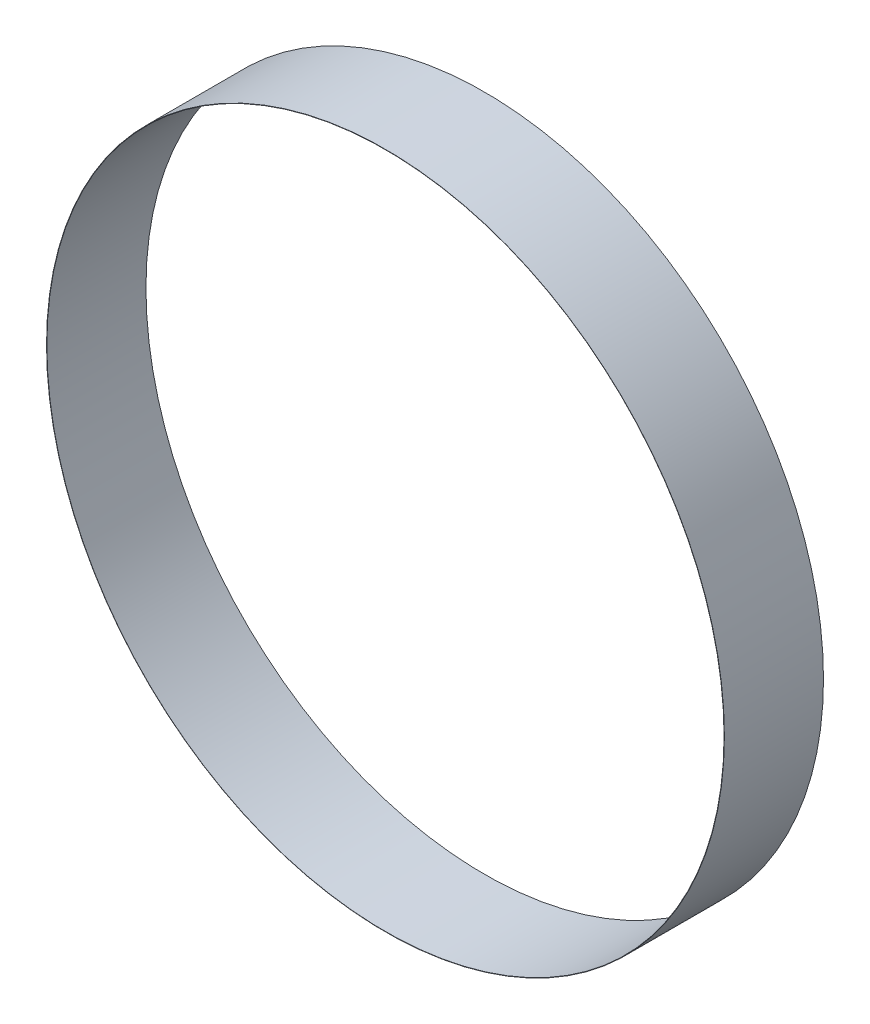
SolidWorks part; units mm, degrees
ref_plane "前视基准面" through (0, 0, 0) normal (0, 0, 1) x (1, 0, 0)
ref_plane "上视基准面" through (0, 0, 0) normal (0, 1, 0) x (1, 0, 0)
ref_plane "右视基准面" through (0, 0, 0) normal (1, 0, 0) x (0, 0, -1)
sketch "草图1" plane through (0, 0, 0) normal (0, 0, 1) x (1, 0, 0)
  circle A0 centre (0, 0) radius 102.5
  circle A1 centre (0, 0) radius 102.6
  dimension "D1" = 205
  dimension "D2" = 0.1
extrude "凸台-拉伸1" add sketch "草图1" along normal blind 30
